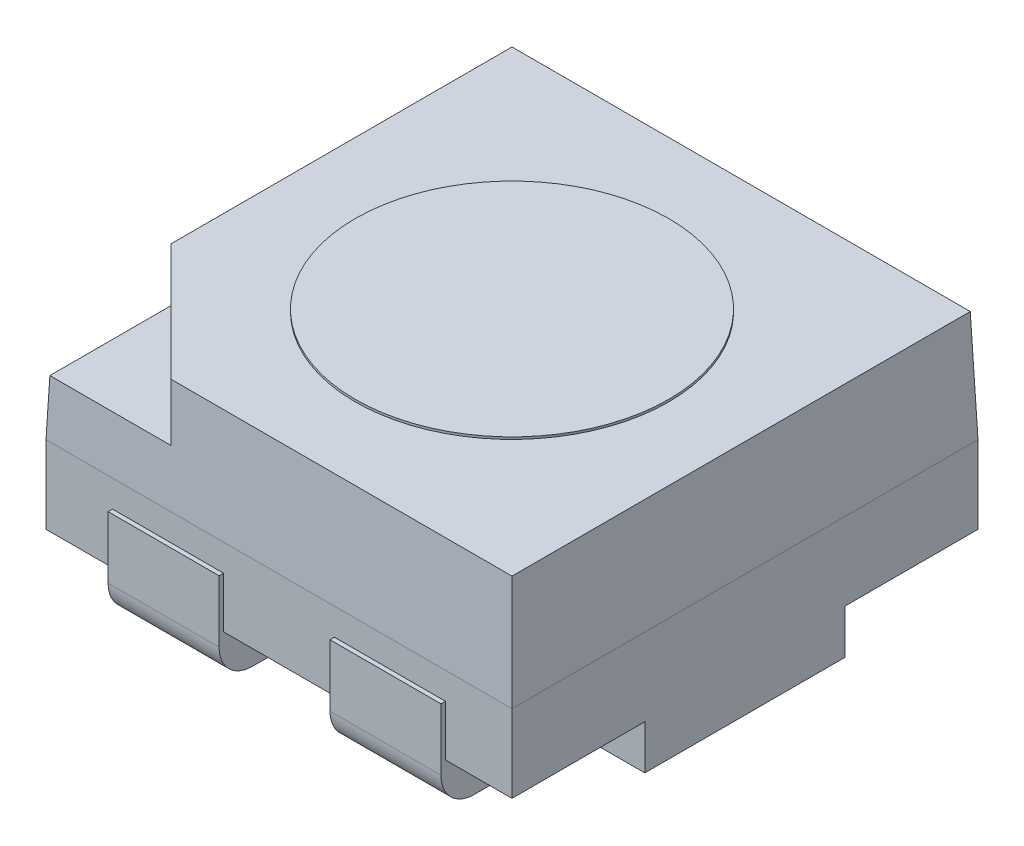
SolidWorks part; units mm, degrees
ref_plane "Plan de face" through (0, 0, 0) normal (0, 0, 1) x (1, 0, 0)
ref_plane "Plan de dessus" through (0, 0, 0) normal (0, 1, 0) x (1, 0, 0)
ref_plane "Plan de droite" through (0, 0, 0) normal (1, 0, 0) x (0, 0, -1)
sketch "Esquisse1" plane through (0, 0, 0) normal (0, 1, 0) x (1, 0, 0)
  line L0 (-2.4601, 0) -> (2.4011, 0) construction
  line L1 (0, 2.3519) -> (0, -2.1551) construction
  line L3 (-1.05, -1.05) -> (1.05, -1.05)
  line L4 (-1.05, -1.05) -> (-1.05, 1.05)
  line L5 (-1.05, 1.05) -> (1.05, 1.05)
  line L6 (1.05, -1.05) -> (1.05, 1.05)
  line L7 (-1.05, -1.05) -> (1.05, 1.05) construction
  line L8 (-1.05, 1.05) -> (1.05, -1.05) construction
  point P5 (0, 0)
  dimension "D1" = 2.1
  dimension "D2" = 2.1
extrude "Boss.-Extru.1" add sketch "Esquisse1" along normal blind 0.35
sketch "Esquisse2" plane through (0, 0.35, 0) normal (0, 1, 0) x (1, 0, 0)
  line L1 (-1.05, -1.05) -> (1.05, -1.05)
  line L2 (-1.05, -1.05) -> (-1.05, 1.05)
  line L3 (-1.05, 1.05) -> (1.05, 1.05)
  line L4 (1.05, -1.05) -> (1.05, 1.05)
  line L5 (-1.05, -1.05) -> (1.05, 1.05) construction
  line L6 (-1.05, 1.05) -> (1.05, -1.05) construction
  point P1 (0, 0)
extrude "Boss.-Extru.2" add sketch "Esquisse2" along normal blind 0.5 draft 2 separate body
sketch "Esquisse3" plane through (0, 0.85, 0) normal (0, 1, 0) x (1, 0, 0)
  circle A0 centre (0, 0) radius 0.706
  point P1 (0, -0.706)
  point P3 (0, 0.706)
extrude "Boss.-Extru.3" add sketch "Esquisse3" along normal blind 0.01
sketch "Esquisse4" plane through (0, 0.85, 0) normal (0, 1, 0) x (1, 0, 0)
  line L0 (1.0942, -1.096) -> (1.0942, -0.4437)
  line L2 (1.0942, -0.4437) -> (0.4395, -1.096)
  line L4 (0.4395, -1.096) -> (1.0942, -1.096)
extrude "Enlèv. mat.-Extru.2" cut sketch "Esquisse4" against normal blind 0.25
sketch "Esquisse5" plane through (0, 0, 0) normal (0, -1, 0) x (1, 0, 0)
  line L0 (0, 0) -> (-2.8715, 0) construction
  line L1 (1.05, 1.05) -> (1.05, -1.05) construction
  line L2 (0.55, 0.25) -> (1.05, 0.25)
  line L3 (0.55, 0.25) -> (0.55, 0.75)
  line L4 (0.55, 0.75) -> (1.05, 0.75)
  line L5 (1.05, 0.25) -> (1.05, 0.75)
  line L6 (0.55, -0.25) -> (1.05, -0.25)
  line L7 (0.55, -0.25) -> (0.55, -0.75)
  line L8 (0.55, -0.75) -> (1.05, -0.75)
  line L9 (1.05, -0.25) -> (1.05, -0.75)
  line L13 (-2.8715, 0) -> (2.2685, 0) construction
  line L14 (0, 1.9164) -> (0, -1.9756) construction
  line L23 (-1.05, 0.25) -> (-0.55, 0.25)
  line L24 (-1.05, 0.25) -> (-1.05, 0.75)
  line L25 (-1.05, 0.75) -> (-0.55, 0.75)
  line L26 (-0.55, 0.25) -> (-0.55, 0.75)
  line L27 (-1.05, 0.25) -> (-0.55, 0.75) construction
  line L28 (-1.05, 0.75) -> (-0.55, 0.25) construction
  line L35 (-1.05, -0.75) -> (-0.55, -0.75)
  line L36 (-1.05, -0.75) -> (-1.05, -0.25)
  line L37 (-1.05, -0.25) -> (-0.55, -0.25)
  line L38 (-0.55, -0.75) -> (-0.55, -0.25)
  line L39 (-1.05, -0.75) -> (-0.55, -0.25) construction
  line L40 (-1.05, -0.25) -> (-0.55, -0.75) construction
  point P23 (-0.8, 0.5)
  point P33 (-0.8, -0.5)
  dimension "D2" = 0.5
  dimension "D3" = 0.55
  dimension "D5" = 0.55
  dimension "D7" = 0.5
  dimension "D10" = 0.5
  dimension "D11" = 0.75
  dimension "D13" = 0.75
  dimension "D15" = 0.5
  dimension "D17" = 0.55
extrude "Boss.-Extru.4" add sketch "Esquisse5" along normal blind 0.2
sketch "Esquisse6" plane through (-1.05, 0, 0) normal (-1, 0, 0) x (0, 0, 1)
  line L1 (-0.75, -0.2) -> (-0.25, -0.2)
  line L2 (-0.75, -0.2) -> (-0.75, 0.2288)
  line L3 (-0.75, 0.2288) -> (-0.25, 0.2288)
  line L4 (-0.25, -0.2) -> (-0.25, 0.2288)
  line L5 (0.25, -0.2) -> (0.75, -0.2)
  line L6 (0.25, -0.2) -> (0.25, 0.2288)
  line L7 (0.25, 0.2288) -> (0.75, 0.2288)
  line L8 (0.75, -0.2) -> (0.75, 0.2288)
extrude "Enlèv. mat.-Extru.3" cut sketch "Esquisse6" against normal blind 0.2
sketch "Esquisse8" plane through (1.05, 0, 0) normal (1, 0, 0) x (0, 0, -1)
  line L1 (-0.75, -0.2) -> (-0.25, -0.2)
  line L2 (-0.75, -0.2) -> (-0.75, 0.2288)
  line L3 (-0.75, 0.2288) -> (-0.25, 0.2288)
  line L4 (-0.25, -0.2) -> (-0.25, 0.2288)
  line L5 (0.25, -0.2) -> (0.75, -0.2)
  line L6 (0.25, -0.2) -> (0.25, 0.2288)
  line L7 (0.25, 0.2288) -> (0.75, 0.2288)
  line L8 (0.75, -0.2) -> (0.75, 0.2288)
extrude "Enlèv. mat.-Extru.4" cut sketch "Esquisse8" against normal blind 0.2
sketch "Esquisse9" plane through (-0.85, 0, 0) normal (-1, 0, 0) x (0, 0, 1)
  line L1 (-0.75, -0.2) -> (-0.25, -0.2)
  line L2 (-0.75, -0.2) -> (-0.75, 0.2288)
  line L3 (-0.75, 0.2288) -> (-0.25, 0.2288)
  line L4 (-0.25, -0.2) -> (-0.25, 0.2288)
  line L5 (0.25, -0.2) -> (0.75, -0.2)
  line L6 (0.25, -0.2) -> (0.25, 0.2288)
  line L7 (0.25, 0.2288) -> (0.75, 0.2288)
  line L8 (0.75, -0.2) -> (0.75, 0.2288)
extrude "Boss.-Extru.5" add sketch "Esquisse9" along normal blind 0.22
sketch "Esquisse10" plane through (0.85, 0, 0) normal (1, 0, 0) x (0, 0, -1)
  line L1 (-0.75, -0.2) -> (-0.25, -0.2)
  line L2 (-0.75, -0.2) -> (-0.75, 0.2288)
  line L3 (-0.75, 0.2288) -> (-0.25, 0.2288)
  line L4 (-0.25, -0.2) -> (-0.25, 0.2288)
  line L5 (0.25, -0.2) -> (0.75, -0.2)
  line L6 (0.25, -0.2) -> (0.25, 0.2288)
  line L7 (0.25, 0.2288) -> (0.75, 0.2288)
  line L8 (0.75, -0.2) -> (0.75, 0.2288)
extrude "Boss.-Extru.6" add sketch "Esquisse10" along normal blind 0.22
sketch "Esquisse12" plane through (0, 0, 0.75) normal (0, 0, 1) x (1, 0, 0)
  line L1 (-1.05, 0) -> (1.05, 0) construction
  line L2 (-0.92, -0.2) -> (-1.2614, -0.2)
  line L3 (-1.07, -0.05) -> (-1.07, 0)
  line L4 (-1.07, 0) -> (-1.2614, 0)
  line L6 (-1.2614, -0.2) -> (-1.2614, 0)
  line L8 (0.92, -0.2) -> (1.2484, -0.2)
  line L9 (1.07, -0.05) -> (1.07, 0)
  line L10 (1.07, 0) -> (1.2484, 0)
  line L11 (1.2484, -0.2) -> (1.2484, 0)
  arc A0 (0.92, -0.2) -> (1.07, -0.05) centre (0.92, -0.05) ccw
  arc A1 (-0.92, -0.2) -> (-1.07, -0.05) centre (-0.92, -0.05) cw
  point P14 (1.07, -0.2)
  point P17 (-1.07, -0.2)
  dimension "D1" = 0.15
extrude "Enlèv. mat.-Extru.5" cut sketch "Esquisse12" against normal through all
sketch "Esquisse13" plane through (0, -0.2, 0) normal (0, -1, 0) x (1, 0, 0)
  point P0 (0, 0)
move or copy body "Corps-Déplacer/Copier1" bodies to move or copy 105 113 copy no rotation origin (0, 0, 0) rotation axis (0, 1, 0) rotation angle 180
sketch "Esquisse14" plane through (0, 0, 0) normal (0, -1, 0) x (-1, 0, 0)
  line L0 (1.05, -1.05) -> (-1.05, -1.05) construction
  line L1 (0.4515, 1.05) -> (-0.4515, 1.05)
  line L2 (0.4515, 1.05) -> (0.4515, -1.05)
  line L3 (0.4515, -1.05) -> (-0.4515, -1.05)
  line L4 (-0.4515, 1.05) -> (-0.4515, -1.05)
  line L5 (0.4515, 1.05) -> (-0.4515, -1.05) construction
  line L6 (0.4515, -1.05) -> (-0.4515, 1.05) construction
  point P0 (0, 0)
extrude "Boss.-Extru.7" add sketch "Esquisse14" along normal blind 0.2
move or copy body "Corps-Déplacer/Copier2" bodies to move or copy 114 122 copy no rotation origin (0, 0, 0) rotation axis (0, 1, 0) rotation angle 90
